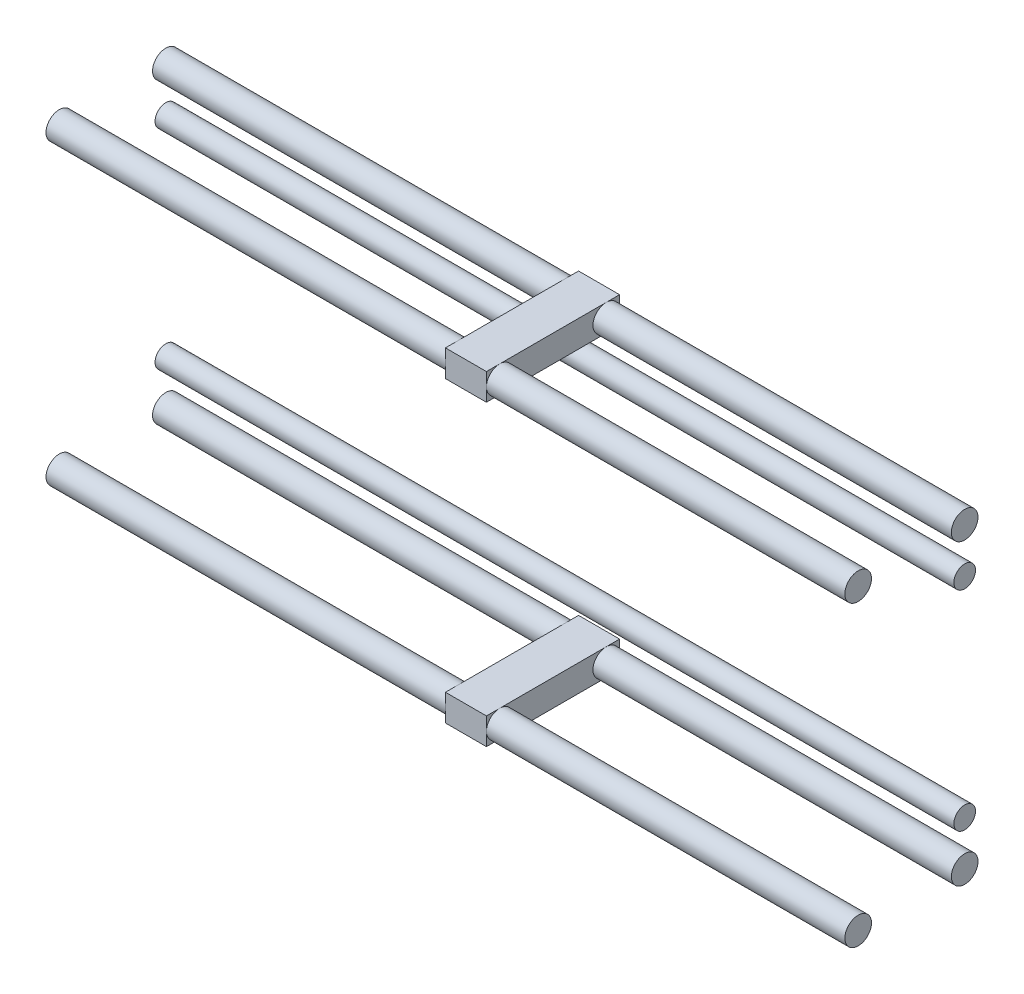
SolidWorks part; units mm, degrees
material "ABS"
ref_plane "Alzado" through (0, 0, 0) normal (0, 0, 1) x (1, 0, 0)
ref_plane "Planta" through (0, 0, 0) normal (0, 1, 0) x (1, 0, 0)
ref_plane "Vista lateral" through (0, 0, 0) normal (1, 0, 0) x (0, 0, -1)
sketch "Croquis1" plane through (0, 0, 0) normal (1, 0, 0) x (0, 0, -1)
  line L1 (-10.3716, 41.8342) -> (14.6284, 41.8342)
  line L2 (-10.3716, 41.8342) -> (-10.3716, 46.8342)
  line L3 (-10.3716, 46.8342) -> (14.6284, 46.8342)
  line L4 (14.6284, 41.8342) -> (14.6284, 46.8342)
  line L6 (-10.3716, -14.1658) -> (14.6284, -14.1658)
  line L7 (-10.3716, -14.1658) -> (-10.3716, -9.1658)
  line L8 (-10.3716, -9.1658) -> (14.6284, -9.1658)
  line L9 (14.6284, -14.1658) -> (14.6284, -9.1658)
  circle A0 centre (-7.8716, 44.3342) radius 2.5
  circle A1 centre (12.1284, 44.3342) radius 2.5
  circle A2 centre (-7.8716, -11.6658) radius 2.5
  circle A3 centre (12.1284, -11.6658) radius 2.5
  point P12 (-14.8318, -7.4257)
  point P15 (0, 0)
  dimension "D1" = 5
  dimension "D2" = 20
  dimension "D3" = 56
extrude "Saliente-Extruir1" add sketch "Croquis1" along normal blind 7.7 contours L8 L9 L6 L7 | L1 L4 L3 L2
sketch "Croquis2" plane through (0, 0, 0) normal (-1, 0, 0) x (0, 0, 1)
  circle A0 centre (-12.1284, 44.3342) radius 2.5
  circle A1 centre (7.8716, 44.3342) radius 2.5
  circle A2 centre (7.8716, -11.6658) radius 2.5
  circle A3 centre (-12.1284, -11.6658) radius 2.5
  circle A4 centre (-12.1284, 35.9342) radius 2.03
  circle A5 centre (-12.1284, -3.2658) radius 2.03
  point P16 (0, 0)
  dimension "D1" = 5
  dimension "D2" = 4.06
  dimension "D3" = 8.4
  dimension "D4" = 8.4
extrude "Saliente-Extruir2" add sketch "Croquis2" along normal mid plane 150
